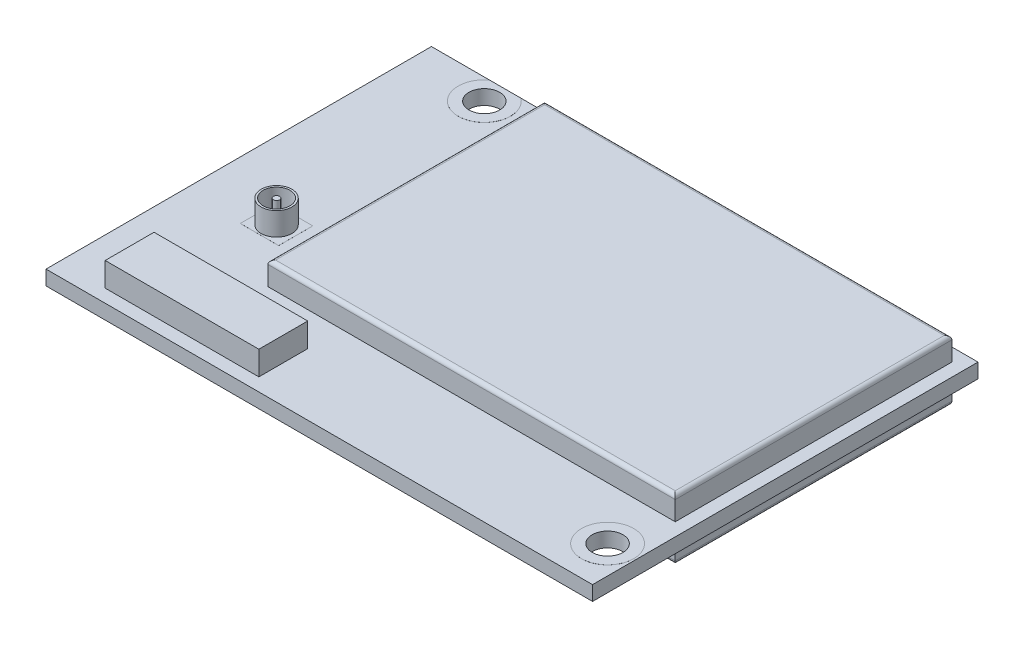
SolidWorks part; units mm, degrees
ref_plane "Front Plane" through (0, 0, 0) normal (0, 0, 1) x (1, 0, 0)
ref_plane "Top Plane" through (0, 0, 0) normal (0, 1, 0) x (1, 0, 0)
ref_plane "Right Plane" through (0, 0, 0) normal (1, 0, 0) x (0, 0, -1)
sketch "Sketch1" plane through (0, 0, 0) normal (0, 1, 0) x (1, 0, 0)
  line L1 (-17.78, 12.54) -> (17.78, 12.54)
  line L2 (-17.78, 12.54) -> (-17.78, -12.54)
  line L3 (-17.78, -12.54) -> (17.78, -12.54)
  line L4 (17.78, 12.54) -> (17.78, -12.54)
  line L5 (-17.78, 12.54) -> (17.78, -12.54) construction
  line L6 (-17.78, -12.54) -> (17.78, 12.54) construction
  point P0 (0, 0)
  dimension "D1" = 35.56
  dimension "D2" = 25.08
extrude "Boss-Extrude1" add sketch "Sketch1" along normal blind 0.95
sketch "Sketch2" plane through (0, 0.95, 0) normal (0, 1, 0) x (1, 0, 0)
  line L2 (16.93, -12.54) -> (16.93, 12.54)
  line L3 (16.93, -6.31) -> (16.93, 11.69)
  line L4 (16.93, -6.31) -> (-9.57, -6.31)
  line L5 (17.78, 11.69) -> (-17.78, 11.69)
  line L6 (16.93, 11.69) -> (-9.57, 11.69)
  line L7 (-9.57, -6.31) -> (-9.57, 11.69)
  line L9 (17.78, 11.69) -> (-17.78, 11.69) construction
  line L10 (17.78, -6.31) -> (-17.78, -6.31) construction
  line L11 (-9.57, -12.54) -> (-9.57, 12.54) construction
  line L12 (16.93, -12.54) -> (16.93, 12.54) construction
  dimension "D1" = 0.85
  dimension "D2" = 0.85
  dimension "D3" = 18
  dimension "D4" = 26.5
extrude "Boss-Extrude2" add sketch "Sketch2" along normal blind 1.5
sketch "Sketch3" plane through (0, 0, 0) normal (0, -1, 0) x (1, 0, 0)
  line L2 (16.93, 12.54) -> (16.93, -12.54)
  line L3 (16.93, 6.31) -> (16.93, -11.69)
  line L4 (-16.47, 6.31) -> (-16.47, -8.69)
  line L5 (17.78, -11.69) -> (-17.78, -11.69)
  line L6 (16.93, -11.69) -> (-11.22, -11.69)
  line L7 (16.93, 6.31) -> (-16.47, 6.31)
  line L8 (-11.22, -8.69) -> (-11.22, -11.69)
  line L9 (17.78, -11.69) -> (-17.78, -11.69) construction
  line L10 (16.93, 12.54) -> (16.93, -12.54) construction
  line L11 (-16.47, 12.54) -> (-16.47, -12.54) construction
  line L12 (17.78, 6.31) -> (-17.78, 6.31) construction
  line L13 (-11.22, -8.69) -> (-16.47, -8.69)
  line L15 (16.93, -8.69) -> (-16.47, -8.69) construction
  line L16 (-11.22, 6.31) -> (-11.22, -11.69) construction
  line L17 (16.93, -11.69) -> (-16.47, -11.69) construction
  line L18 (-16.47, 6.31) -> (-16.47, -11.69) construction
  dimension "D1" = 0.85
  dimension "D2" = 0.85
  dimension "D3" = 33.4
  dimension "D4" = 18
  dimension "D5" = 5.25
  dimension "D6" = 3
extrude "Boss-Extrude3" add sketch "Sketch3" along normal blind 1.5
sketch "Sketch4" plane through (0, 0.95, 0) normal (0, 1, 0) x (1, 0, 0)
  line L2 (-14.78, 12.54) -> (-14.78, -12.54)
  line L3 (-14.78, -8.51) -> (-14.78, -11.69)
  line L4 (-4.78, -8.51) -> (-4.78, -11.69)
  line L5 (-17.78, -11.69) -> (17.78, -11.69)
  line L6 (-14.78, -11.69) -> (-4.78, -11.69)
  line L7 (-14.78, -8.51) -> (-4.78, -8.51)
  line L9 (-14.78, 12.54) -> (-14.78, -12.54) construction
  line L10 (-17.78, -8.51) -> (17.78, -8.51) construction
  line L11 (-17.78, -11.69) -> (17.78, -11.69) construction
  line L12 (-4.78, 12.54) -> (-4.78, -12.54) construction
  dimension "D1" = 3
  dimension "D2" = 0.85
  dimension "D3" = 10
  dimension "D4" = 3.18
extrude "Boss-Extrude4" add sketch "Sketch4" along normal blind 1.56
sketch "Sketch5" plane through (0, 0.95, 0) normal (0, 1, 0) x (1, 0, 0)
  line L2 (-12.78, 12.54) -> (-12.78, -12.54)
  line L3 (-12.78, -2.54) -> (-12.78, -12.54) construction
  line L5 (-17.78, -2.54) -> (17.78, -2.54)
  line L6 (-17.78, -2.54) -> (-12.78, -2.54) construction
  circle A0 centre (-12.78, -2.54) radius 1
  circle A1 centre (-12.78, -2.54) radius 0.2
  circle A2 centre (-12.78, -2.54) radius 0.875
  dimension "D3" = 2
  dimension "D4" = 0.4
  dimension "D1" = 5
  dimension "D2" = 10
  dimension "D5" = 0.125
extrude "Boss-Extrude5" add sketch "Sketch5" along normal blind 1.5 contours A0 A2 | A1
sketch "Sketch6" plane through (0, 0, 0) normal (0, -1, 0) x (1, 0, 0)
  line L1 (-2.02, 10.24) -> (-2.02, 8.39)
  line L2 (13.48, 12.54) -> (13.48, -12.54)
  line L3 (13.48, 10.24) -> (13.48, 8.39)
  line L5 (-2.02, 8.39) -> (13.48, 8.39)
  line L6 (-17.78, 10.24) -> (17.78, 10.24)
  line L7 (-2.02, 10.24) -> (13.48, 10.24)
  line L8 (-1.77, 8.64) -> (13.23, 8.64)
  line L9 (13.48, 12.54) -> (13.48, -12.54) construction
  line L10 (-2.02, 12.54) -> (-2.02, -12.54) construction
  line L11 (-17.78, 10.24) -> (17.78, 10.24) construction
  line L12 (-17.78, 8.39) -> (17.78, 8.39) construction
  line L13 (13.23, 9.99) -> (13.23, 8.64)
  line L14 (-1.77, 9.99) -> (13.23, 9.99)
  line L15 (-1.77, 9.99) -> (-1.77, 8.64)
  dimension "D1" = 4.3
  dimension "D2" = 15.5
  dimension "D3" = 2.3
  dimension "D4" = 1.85
  dimension "D5" = 0.25
extrude "Boss-Extrude6" add sketch "Sketch6" along normal blind 0.75
sketch "Sketch7" plane through (0, 0, 0) normal (0, -1, 0) x (1, 0, 0)
  line L2 (15.96, 12.54) -> (15.96, -12.54)
  line L3 (15.96, 12.54) -> (15.96, 9.74) construction
  line L5 (-17.78, 9.74) -> (17.78, 9.74)
  line L6 (15.96, 9.74) -> (17.78, 9.74) construction
  circle A0 centre (15.96, 9.74) radius 1
  dimension "D3" = 2
  dimension "D1" = 1.82
  dimension "D2" = 2.8
extrude "Cut-Extrude1" cut sketch "Sketch7" against normal through all
sketch "Sketch8" plane through (0, 0.95, 0) normal (0, 1, 0) x (1, 0, 0)
  line L2 (-12.98, 12.54) -> (-12.98, -12.54)
  line L3 (-12.98, 12.54) -> (-12.98, 11.18) construction
  line L5 (17.78, 11.18) -> (-17.78, 11.18)
  line L6 (-12.98, 11.18) -> (-17.78, 11.18) construction
  circle A0 centre (-12.98, 11.18) radius 1
  dimension "D3" = 2
  dimension "D1" = 4.8
  dimension "D2" = 1.36
extrude "Cut-Extrude2" cut sketch "Sketch8" against normal through all
sketch "Sketch9" plane through (0, 0.95, 0) normal (0, 1, 0) x (1, 0, 0)
  line L0 (17.78, 12.54) -> (-17.78, 12.54) construction
  line L1 (-11.96, 12.54) -> (-14, 12.54)
  circle A2 centre (-12.98, 11.18) radius 1.7
  arc A3 (-14, 12.54) -> (-11.96, 12.54) centre (-12.98, 11.18) ccw
  circle A4 centre (-12.98, 11.18) radius 1 construction
  circle A5 centre (15.96, -9.74) radius 1.7
  circle A6 centre (15.96, -9.74) radius 1.7
  circle A7 centre (15.96, -9.74) radius 1 construction
  circle A8 centre (-12.98, 11.18) radius 1
  circle A9 centre (15.96, -9.74) radius 1
  dimension "D1" = 0.7
  dimension "D2" = 0.7
extrude "Boss-Extrude7" add sketch "Sketch9" along normal blind 0.0025
sketch "Sketch10" plane through (0, 0, 0) normal (0, -1, 0) x (1, 0, 0)
  line L0 (-11.96, -12.54) -> (-14, -12.54) construction
  line L1 (-11.96, -12.54) -> (-14, -12.54)
  arc A0 (-11.96, -12.54) -> (-14, -12.54) centre (-12.98, -11.18) ccw construction
  circle A1 centre (15.96, 9.74) radius 1.7 construction
  arc A2 (-11.96, -12.54) -> (-14, -12.54) centre (-12.98, -11.18) ccw
  circle A3 centre (15.96, 9.74) radius 1.7
  circle A4 centre (-12.98, -11.18) radius 1 construction
  circle A5 centre (15.96, 9.74) radius 1 construction
  circle A6 centre (-12.98, -11.18) radius 1
  circle A7 centre (15.96, 9.74) radius 1
extrude "Boss-Extrude8" add sketch "Sketch10" along normal blind 0.0025 and the other way up to surface
fillet "Fillet1" radius 0.25 10 edges at (-11.22, -1.5, -10.19) (-13.845, -1.5, -8.69) (-16.47, -1.5, -1.19) (0.23, -1.5, 6.31) (16.93, -1.5, -2.69) (2.855, -1.5, -11.69) (3.68, 2.45, -11.69) (16.93, 2.45, -2.69) (3.68, 2.45, 6.31) (-9.57, 2.45, -2.69)
sketch "Sketch11" plane through (0, 0.95, 0) normal (0, 1, 0) x (1, 0, 0)
  line L1 (-14.0271, -1.4302) -> (-11.5329, -1.4302)
  line L2 (-14.0271, -1.4302) -> (-14.0271, -3.6498)
  line L3 (-14.0271, -3.6498) -> (-11.5329, -3.6498)
  line L4 (-11.5329, -1.4302) -> (-11.5329, -3.6498)
  line L5 (-14.0271, -1.4302) -> (-11.5329, -3.6498) construction
  line L6 (-14.0271, -3.6498) -> (-11.5329, -1.4302) construction
  point P0 (-12.78, -2.54)
extrude "Boss-Extrude9" add sketch "Sketch11" along normal blind 0.0025
